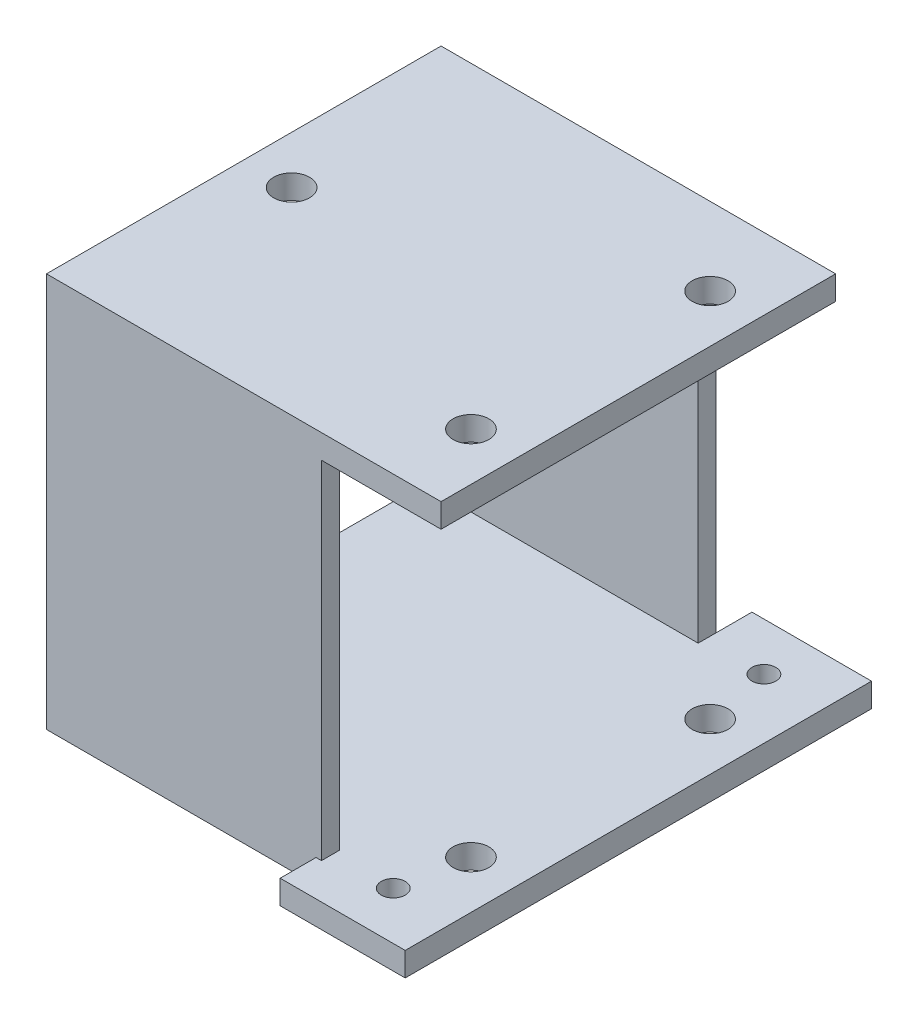
SolidWorks part; units mm, degrees
ref_plane "Front Plane" through (0, 0, 0) normal (0, 0, 1) x (1, 0, 0)
ref_plane "Top Plane" through (0, 0, 0) normal (0, 1, 0) x (1, 0, 0)
ref_plane "Right Plane" through (0, 0, 0) normal (1, 0, 0) x (0, 0, -1)
sketch "Sketch1" plane through (0, 0, 0) normal (0, 1, 0) x (1, 0, 0)
  line L0 (-14.9876, -24.4514) -> (-4.5322, -24.4514)
  line L1 (-37.5322, 8.5486) -> (-4.5322, 8.5486)
  line L2 (-37.5322, 8.5486) -> (-37.5322, -24.4514)
  line L3 (-37.5322, -24.4514) -> (-4.5322, -24.4514)
  line L4 (-4.5322, 8.5486) -> (-4.5322, -24.4514)
  line L5 (-14.5322, 11.5486) -> (-4.5322, 11.5486)
  line L6 (-14.5322, 11.5486) -> (-14.5322, 8.5486)
  line L7 (-14.5322, 8.5486) -> (-4.5322, 8.5486)
  line L8 (-4.5322, 11.5486) -> (-4.5322, 8.5486)
  line L9 (-14.9876, -24.4514) -> (-14.9876, -27.4514)
  line L10 (-14.9876, -27.4514) -> (-4.5322, -27.4514)
  line L11 (-4.5322, -24.4514) -> (-4.5322, -27.4514)
  dimension "D1" = 33
  dimension "D2" = 33
  dimension "D3" = 3
  dimension "D4" = 10
  dimension "D5" = 0
  dimension "D6" = 0
  dimension "D7" = 0
  dimension "D8" = 0
extrude "Boss-Extrude1" add sketch "Sketch1" along normal blind 2 contours L2 L1 L4 L3 | L0 L11 L10 L9 | L5 L8 L7 L6
sketch "Sketch2" plane through (0, 2, 0) normal (0, 1, 0) x (1, 0, 0)
  line L0 (-4.5322, 11.5486) -> (-4.5322, -27.4514) construction
  line L1 (-14.9876, -27.4514) -> (-4.5322, -27.4514) construction
  line L2 (-14.5322, 11.5486) -> (-4.5322, 11.5486) construction
  circle A0 centre (-9.5322, 7.5486) radius 1
  circle A1 centre (-9.5322, -23.4514) radius 1
  point P14 (0, 0)
  point P15 (0, 0)
  dimension "D1" = 2
  dimension "D2" = 2
  dimension "D3" = 5
  dimension "D4" = 5
  dimension "D5" = 4
  dimension "D6" = 4
extrude "Cut-Extrude2" cut sketch "Sketch2" against normal through all
sketch3d "3DSketch1"
  line L0 (-37.5322, 2, 24.4514) -> (-14.9876, 2, 24.4514) construction
  line L1 (-37.5322, 2, 22.9514) -> (-37.5322, 2, 24.4514)
  line L2 (-37.5322, 2, 22.9514) -> (-14.5322, 2, 22.9514)
  line L3 (-14.5322, 2, 22.9514) -> (-14.5322, 2, 24.4514)
  line L4 (-37.5322, 2, 24.4514) -> (-14.5322, 2, 24.4514)
  line L5 (-37.5322, 2, -8.5486) -> (-37.5322, 2, 24.4514) construction
  line L6 (-37.5322, 2, -8.5486) -> (-14.5322, 2, -8.5486) construction
  line L7 (-14.5322, 2, -8.5486) -> (-14.5322, 2, -7.0486)
  line L8 (-14.5322, 2, -8.5486) -> (-37.5322, 2, -8.5486)
  line L9 (-37.5322, 2, -8.5486) -> (-37.5322, 2, -7.0486)
  line L10 (-14.5322, 2, -7.0486) -> (-37.5322, 2, -7.0486)
  point P4 (-14.5322, 2, 23.7014)
  point P15 (0, 0, 0)
  dimension "D1" = 1.5
  dimension "D2" = 23
  dimension "D3" = 0
  dimension "D4" = 1.5
  dimension "D5" = 0
  dimension "D6" = 23
  dimension "D7" = 0
  dimension "D8" = 0
extrude "Boss-Extrude3" add sketch "3DSketch1" along direction (0, -1, 0) on the side against the normal blind 29
sketch "Sketch3" plane through (0, 31, 0) normal (0, 1, 0) x (1, 0, 0)
  line L0 (-14.5322, 8.5486) -> (-37.5322, 8.5486) construction
  line L1 (-37.5322, 8.5486) -> (-4.5322, 8.5486)
  line L2 (-37.5322, 8.5486) -> (-37.5322, -24.4514)
  line L3 (-37.5322, -24.4514) -> (-4.5322, -24.4514)
  line L4 (-4.5322, 8.5486) -> (-4.5322, -24.4514)
  line L5 (-37.5322, -24.4514) -> (-37.5322, -22.9514) construction
  dimension "D1" = 33
  dimension "D2" = 33
  dimension "D3" = 0
  dimension "D4" = 0
extrude "Boss-Extrude4" add sketch "Sketch3" along normal blind 2
sketch "Sketch4" plane through (0, 33, 0) normal (0, 1, 0) x (1, 0, 0)
  line L0 (-4.5322, 8.5486) -> (-37.5322, 8.5486) construction
  line L1 (-37.5322, -24.4514) -> (-4.5322, -24.4514) construction
  line L2 (-4.5322, -24.4514) -> (-4.5322, 8.5486) construction
  line L3 (-37.5322, 8.5486) -> (-37.5322, -24.4514) construction
  circle A0 centre (-8.5322, -17.9514) radius 1.5
  circle A1 centre (-8.5322, 2.0486) radius 1.5
  circle A2 centre (-33.5322, -7.9514) radius 1.5
  dimension "D1" = 3
  dimension "D2" = 3
  dimension "D3" = 3
  dimension "D4" = 20
  dimension "D5" = 6.5
  dimension "D6" = 16.5
  dimension "D7" = 4
  dimension "D8" = 4
  dimension "D9" = 4
extrude "Cut-Extrude4" cut sketch "Sketch4" against normal through all
